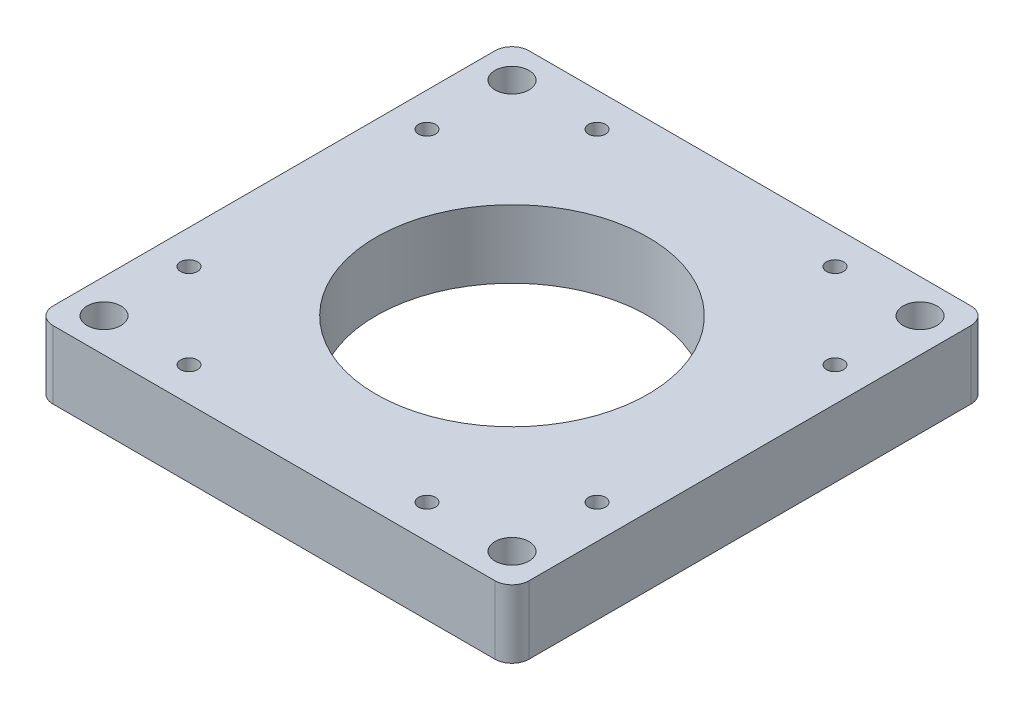
SolidWorks part; units mm, degrees
ref_plane "Front Plane" through (0, 0, 0) normal (0, 0, 1) x (1, 0, 0)
ref_plane "Top Plane" through (0, 0, 0) normal (0, 1, 0) x (1, 0, 0)
ref_plane "Right Plane" through (0, 0, 0) normal (1, 0, 0) x (0, 0, -1)
sketch "Sketch1" plane through (0, 0, 0) normal (0, 1, 0) x (1, 0, 0)
  line L0 (-1000, 0) -> (49000, 0) construction
  line L1 (0, -1000) -> (0, 49000) construction
  line L3 (76.2, -76.2) -> (-76.2, -76.2) construction
  line L4 (76.2, -76.2) -> (76.2, 76.2) construction
  line L5 (76.2, 76.2) -> (-76.2, 76.2) construction
  line L6 (-76.2, -76.2) -> (-76.2, 76.2) construction
  line L7 (76.2, -76.2) -> (-76.2, 76.2) construction
  line L8 (76.2, 76.2) -> (-76.2, -76.2) construction
  line L9 (88.9, -88.9) -> (-88.9, -88.9)
  line L10 (88.9, -88.9) -> (88.9, 88.9)
  line L11 (88.9, 88.9) -> (-88.9, 88.9)
  line L12 (-88.9, -88.9) -> (-88.9, 88.9)
  line L13 (88.9, -88.9) -> (-88.9, 88.9) construction
  line L14 (88.9, 88.9) -> (-88.9, -88.9) construction
  arc A0 (-88.9, 0) -> (-76.2, -45.7905) centre (0, 0) ccw construction
  circle A1 centre (0, 0) radius 50.8
  circle A2 centre (44.45, 76.2) radius 3.175
  circle A3 centre (-44.45, 76.2) radius 3.175
  arc A4 (-76.2, 45.7905) -> (-88.9, 0) centre (0, 0) ccw construction
  arc A5 (-62.8618, 62.8618) -> (-76.2, 45.7905) centre (0, 0) ccw construction
  arc A6 (-45.7905, 76.2) -> (-62.8618, 62.8618) centre (0, 0) ccw construction
  arc A7 (0, 88.9) -> (-45.7905, 76.2) centre (0, 0) ccw construction
  arc A8 (45.7905, 76.2) -> (0, 88.9) centre (0, 0) ccw construction
  arc A9 (62.8618, 62.8618) -> (45.7905, 76.2) centre (0, 0) ccw construction
  arc A10 (76.2, 45.7905) -> (62.8618, 62.8618) centre (0, 0) ccw construction
  arc A11 (88.9, 0) -> (76.2, 45.7905) centre (0, 0) ccw construction
  arc A12 (76.2, -45.7905) -> (88.9, 0) centre (0, 0) ccw construction
  arc A13 (62.8618, -62.8618) -> (76.2, -45.7905) centre (0, 0) ccw construction
  arc A14 (45.7905, -76.2) -> (62.8618, -62.8618) centre (0, 0) ccw construction
  arc A15 (0, -88.9) -> (45.7905, -76.2) centre (0, 0) ccw construction
  arc A16 (-45.7905, -76.2) -> (0, -88.9) centre (0, 0) ccw construction
  arc A17 (-62.8618, -62.8618) -> (-45.7905, -76.2) centre (0, 0) ccw construction
  arc A18 (-76.2, -45.7905) -> (-62.8618, -62.8618) centre (0, 0) ccw construction
  circle A19 centre (-76.2, 76.2) radius 6.35
  circle A20 centre (-76.2, -76.2) radius 6.35
  circle A21 centre (76.2, -76.2) radius 6.35
  circle A22 centre (76.2, 76.2) radius 6.35
  circle A23 centre (76.2, 44.45) radius 3.175
  circle A24 centre (76.2, -44.45) radius 3.175
  circle A25 centre (44.45, -76.2) radius 3.175
  circle A26 centre (-44.45, -76.2) radius 3.175
  circle A27 centre (-76.2, -44.45) radius 3.175
  circle A28 centre (-76.2, 44.45) radius 3.175
  point P54 (0, 0)
  dimension "D1" = 177.8
  dimension "D2" = 101.6
  dimension "D5" = 6.35
  dimension "D6" = 6.35
  dimension "D7" = 44.45
  dimension "D9" = 12.7
  dimension "D10" = 12.7
  dimension "D11" = 12.7
  dimension "D12" = 12.7
  dimension "D3" = 152.4
  dimension "D4" = 152.4
  dimension "D8" = 44.45
  dimension "D13" = 177.8
  dimension "D14" = 4
extrude "Boss-Extrude1" add sketch "Sketch1" along normal blind 25.4
fillet "Fillet1" radius 6.35 4 edges at (88.9, 12.7, -88.9) (-88.9, 12.7, -88.9) (88.9, 12.7, 88.9) (-88.9, 12.7, 88.9)
